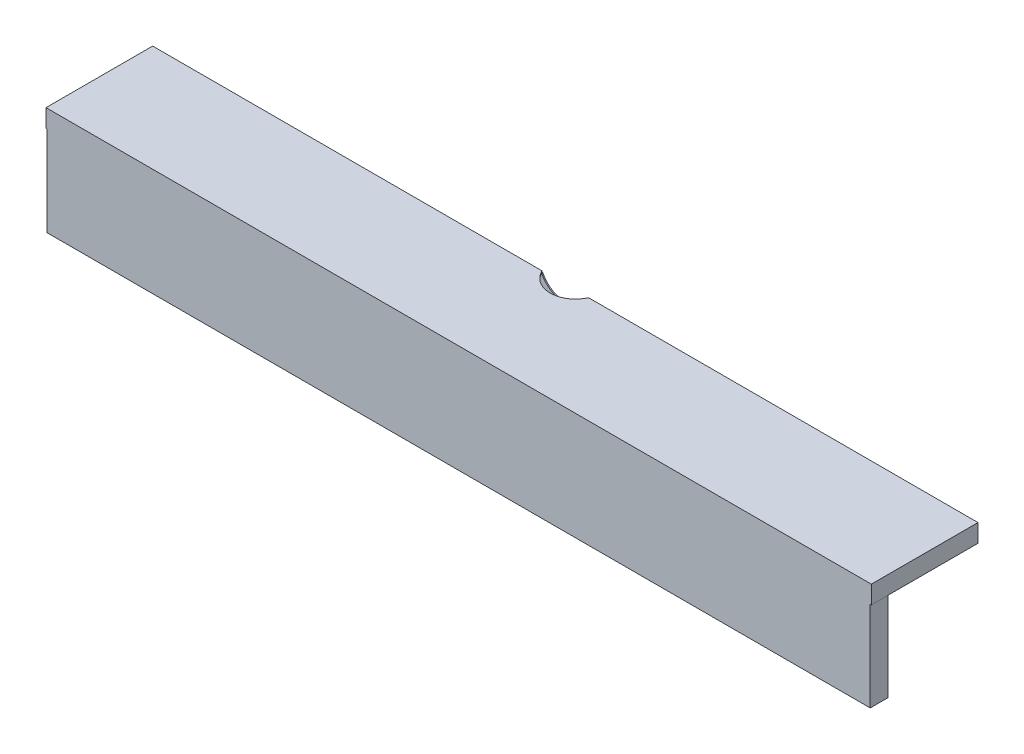
SolidWorks part; units mm, degrees
ref_plane "Alzado" through (0, 0, 0) normal (0, 0, 1) x (1, 0, 0)
ref_plane "Planta" through (0, 0, 0) normal (0, 1, 0) x (1, 0, 0)
ref_plane "Vista lateral" through (0, 0, 0) normal (1, 0, 0) x (0, 0, -1)
sketch "Croquis1" plane through (0, 0, 0) normal (0, 1, 0) x (1, 0, 0)
  line L1 (-367.5, -47.5) -> (367.5, -47.5)
  line L2 (-367.5, -47.5) -> (-367.5, 47.5)
  line L3 (-367.5, 47.5) -> (367.5, 47.5)
  line L4 (367.5, -47.5) -> (367.5, 47.5)
  line L5 (-367.5, -47.5) -> (367.5, 47.5) construction
  line L6 (-367.5, 47.5) -> (367.5, -47.5) construction
  point P0 (0, 0)
  dimension "D1" = 735
  dimension "D2" = 95
extrude "Saliente-Extruir1" add sketch "Croquis1" along normal blind 1
sketch "Croquis2" plane through (0, 0, 0) normal (0, -1, 0) x (1, 0, 0)
  line L0 (-367.5, 47.5) -> (367.5, 47.5) construction
  line L2 (366.5, 47.5) -> (366.5, -46.5)
  line L3 (366.5, -46.5) -> (-366.5, -46.5)
  line L4 (-366.5, 47.5) -> (-366.5, -46.5)
  line L5 (-366.5, 47.5) -> (-367.5, 47.5)
  line L6 (367.5, 47.5) -> (366.5, 47.5)
  line L7 (367.5, 47.5) -> (367.5, -47.5)
  line L8 (367.5, -47.5) -> (-367.5, -47.5)
  line L9 (-367.5, 47.5) -> (-367.5, -47.5)
  dimension "D1" = 1
  dimension "D2" = 1
  dimension "D3" = 1
extrude "Saliente-Extruir2" add sketch "Croquis2" along normal blind 15
sketch "Croquis3" plane through (0, 0, -47.5) normal (0, 0, -1) x (-1, 0, 0)
  line L1 (0, 0) -> (0, 10) construction
  circle A0 centre (0, 10) radius 22.5
  dimension "D1" = 45
  dimension "D2" = 10
extrude "Cortar-Extruir1" cut sketch "Croquis3" against normal up to surface (1 mm away) up to face at (0, -7.5, -46.5)
sketch "Croquis4" plane through (0, 1, 0) normal (0, 1, 0) x (1, 0, 0)
  line L1 (0, 56.5) -> (0, 0) construction
  circle A0 centre (0, 56.5) radius 22.5
  dimension "D1" = 45
extrude "Cortar-Extruir2" cut sketch "Croquis4" against normal up to surface (1 mm away) up to face at (-61.0833, 0, -15.1667)
sketch "Croquis5" plane through (0, 0, 0) normal (0, -1, 0) x (1, 0, 0)
  line L0 (-20.1556, -46.5) -> (-366.5, -46.5) construction
  line L1 (-26, -46.5) -> (-25, -46.5)
  line L2 (-26, -46.5) -> (-26, -31.5)
  line L3 (-26, -31.5) -> (-25, -31.5)
  line L4 (-25, -46.5) -> (-25, -31.5)
  line L5 (366.5, -46.5) -> (20.1556, -46.5) construction
  line L6 (25, -46.5) -> (26, -46.5)
  line L7 (25, -46.5) -> (25, -31.5)
  line L8 (25, -31.5) -> (26, -31.5)
  line L9 (26, -46.5) -> (26, -31.5)
  line L10 (-25, -39) -> (25, -39) construction
  line L11 (0, -39) -> (0, 0) construction
  dimension "D1" = 1
  dimension "D2" = 15
  dimension "D3" = 50
extrude "Saliente-Extruir3" add sketch "Croquis5" along normal blind 15
sketch "Croquis6" plane through (-25, 0, 0) normal (1, 0, 0) x (0, 0, -1)
  line L0 (46.5, -15) -> (46.5, 0) construction
  line L1 (31.5, -15) -> (46.5, -15)
  line L2 (31.5, -15) -> (31.5, -14)
  line L3 (31.5, -14) -> (46.5, -14)
  line L4 (46.5, -15) -> (46.5, -14)
  dimension "D1" = 1
extrude "Saliente-Extruir4" add sketch "Croquis6" along normal up to next
sketch "Croquis7" plane through (0, -15, 0) normal (0, -1, 0) x (1, 0, 0)
  line L0 (-6.5486, -36.9619) -> (6.5486, -36.9619) construction
  line L1 (-6.5486, -34.9091) -> (6.5486, -34.9091)
  line L2 (-6.5486, -39.0148) -> (6.5486, -39.0148)
  line L3 (0, -36.9619) -> (0, 0) construction
  arc A0 (-6.5486, -34.9091) -> (-6.5486, -39.0148) centre (-6.5486, -36.9619) ccw
  arc A1 (6.5486, -39.0148) -> (6.5486, -34.9091) centre (6.5486, -36.9619) ccw
  point P2 (0, -36.9619)
extrude "Cortar-Extruir3" cut sketch "Croquis7" against normal up to next
sketch "Croquis8" plane through (366.5, 0, 0) normal (-1, 0, 0) x (0, 0, 1)
  line L1 (47.5, 0) -> (46.5, 0)
  line L2 (47.5, 0) -> (47.5, -95)
  line L3 (47.5, -95) -> (46.5, -95)
  line L4 (46.5, 0) -> (46.5, -95)
  dimension "D1" = 95
  dimension "D2" = 1
extrude "Saliente-Extruir5" add sketch "Croquis8" along normal up to surface (733 mm away) up to face at (-366.5, -9.375, -11.25)
sketch "Croquis9" plane through (0, 0, 46.5) normal (0, 0, -1) x (-1, 0, 0)
  line L0 (-366.5, -15) -> (-366.5, -95) construction
  line L1 (-366.5, -15.8904) -> (-365.5, -15.8904)
  line L2 (-366.5, -15.8904) -> (-366.5, -95)
  line L3 (-366.5, -95) -> (366.5, -95)
  line L4 (366.5, -15.8904) -> (366.5, -95)
  line L5 (365.5, -15.8904) -> (366.5, -15.8904)
  line L7 (-365.5, -15.8904) -> (-365.5, -94)
  line L8 (-365.5, -94) -> (365.5, -94)
  line L9 (365.5, -15.8904) -> (365.5, -94)
  dimension "D1" = 1
  dimension "D2" = 1
extrude "Saliente-Extruir6" add sketch "Croquis9" along normal blind 15
sketch "Croquis10" plane through (-366.5, 0, 0) normal (-1, 0, 0) x (0, 0, 1)
  line L0 (47.5, -89) -> (31.5, -89) construction
  line L1 (47.5, -95) -> (47.5, -15) construction
  line L2 (31.5, -95) -> (31.5, -15.8904) construction
  line L3 (31.5, -95) -> (47.5, -95) construction
  circle A0 centre (39.5, -89) radius 1.5
  dimension "D2" = 3
  dimension "D1" = 6
extrude "Saliente-Extruir7" add sketch "Croquis10" along normal blind 3.5
